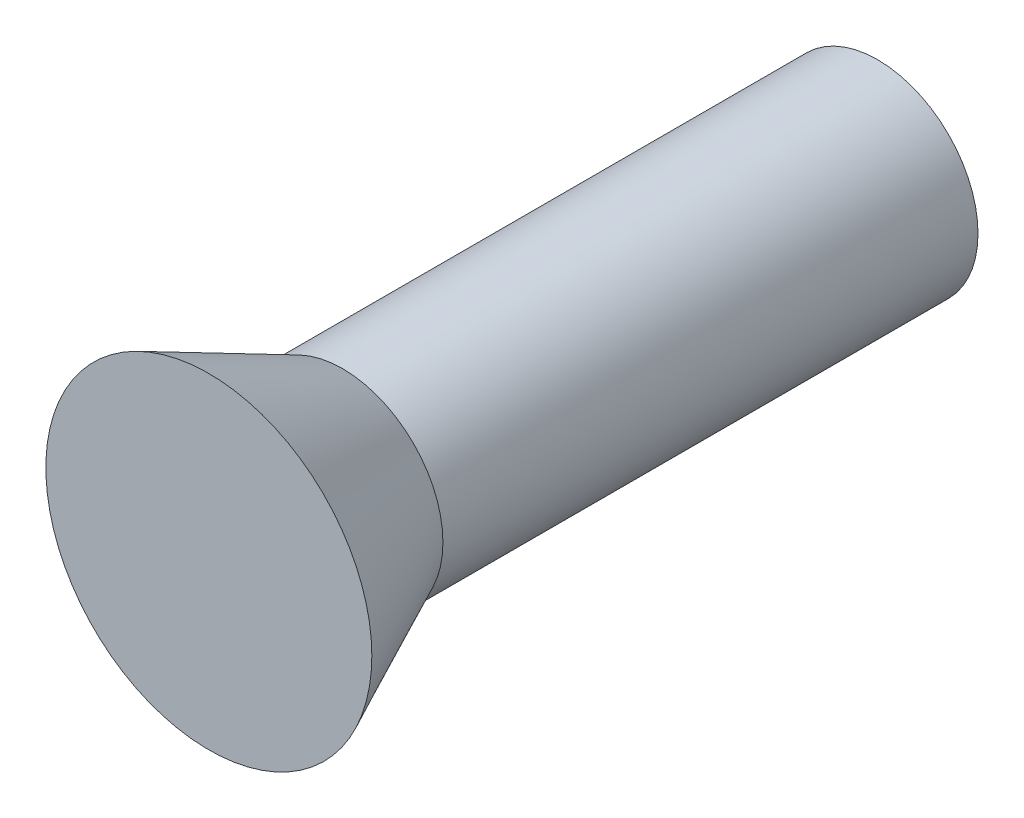
SolidWorks part; units mm, degrees
ref_plane "Спереди" through (0, 0, 0) normal (0, 0, 1) x (1, 0, 0)
ref_plane "Сверху" through (0, 0, 0) normal (0, 1, 0) x (1, 0, 0)
ref_plane "Справа" through (0, 0, 0) normal (1, 0, 0) x (0, 0, -1)
sketch "Эскиз1" plane through (0, 0, 0) normal (0, 1, 0) x (1, 0, 0)
  line L0 (0, 0) -> (0, 10) construction
  line L1 (0, 10) -> (1.5, 10)
  line L2 (1.5, 10) -> (1.5, 2)
  line L3 (1.5, 2) -> (2.4371, 0)
  line L4 (2.4371, 0) -> (0, 0)
  line L5 (0, 0) -> (0, 10)
  dimension "D1" = 10
  dimension "D2" = 3
  dimension "D3" = 2
revolve "Повернуть1" add sketch "Эскиз1" angle 360 about L0
